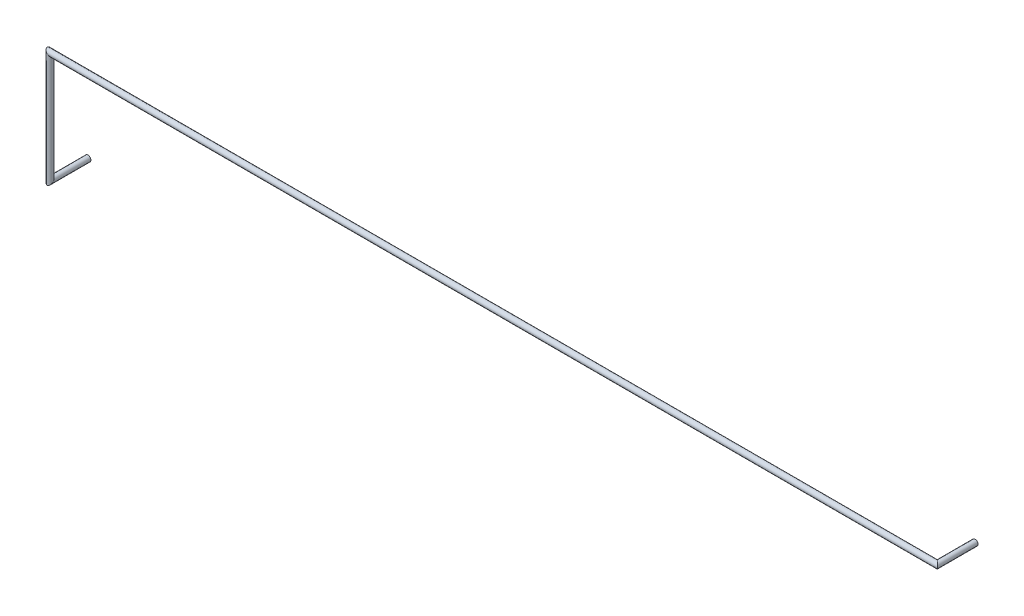
SolidWorks part; units mm, degrees
ref_plane "Front Plane" through (0, 0, 0) normal (0, 0, 1) x (1, 0, 0)
ref_plane "Top Plane" through (0, 0, 0) normal (0, 1, 0) x (1, 0, 0)
ref_plane "Right Plane" through (0, 0, 0) normal (1, 0, 0) x (0, 0, -1)
sketch3d "3DSketch3"
  line L0 (0, 0, 0) -> (0, 0, 2.6)
  line L1 (0, 0, 2.6) -> (0, 7.62, 2.6)
  line L2 (0, 7.62, 2.6) -> (60.96, 7.62, 2.6)
  line L3 (60.96, 7.62, 2.6) -> (60.96, 7.62, 0)
  dimension "D2" = 2.6
  dimension "D1" = 2.6
  dimension "D3" = 7.62
  dimension "D4" = 60.96
sweep "Sweep1" add path "3DSketch3" circular profile diameter 0.4 parameters "D3"=0.4
equation "\"D2@3DSketch3\"=\"D1@3DSketch3\""
equation "\"D3@3DSketch3\"=2.54*3"
equation "\"D4@3DSketch3\"=2.54*24"
